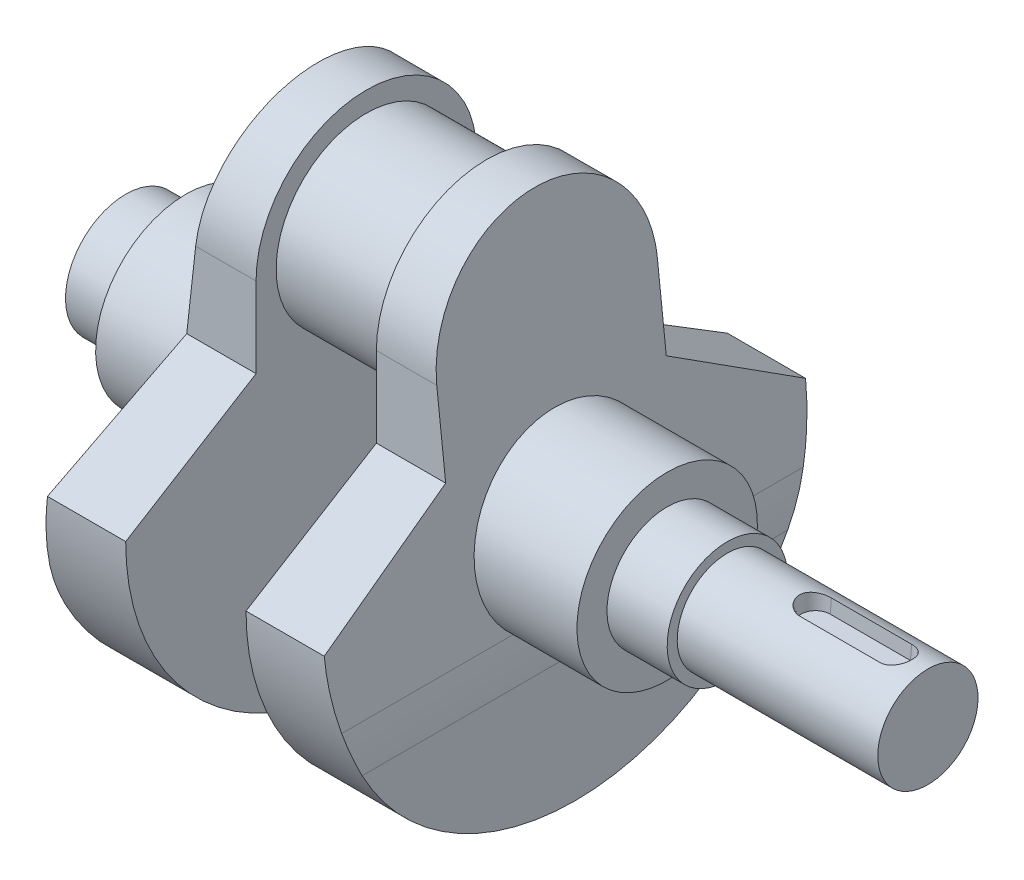
SolidWorks part; units mm, degrees
ref_plane "Front Plane" through (0, 0, 0) normal (0, 0, 1) x (1, 0, 0)
ref_plane "Top Plane" through (0, 0, 0) normal (0, 1, 0) x (1, 0, 0)
ref_plane "Right Plane" through (0, 0, 0) normal (1, 0, 0) x (0, 0, -1)
sketch "Sketch1" plane through (0, 0, 0) normal (1, 0, 0) x (0, 0, -1)
  circle A0 centre (0, 0) radius 22.5
  dimension "D1" = 45
extrude "Boss-Extrude1" add sketch "Sketch1" along normal blind 15
sketch "Sketch2" plane through (15, 0, 0) normal (1, 0, 0) x (0, 0, -1)
  line L0 (-27.5, 0) -> (-27.5, -20)
  line L1 (-27.5, -20) -> (-60, -40)
  line L2 (0, 0) -> (0, -100) construction
  line L3 (27.5, -20) -> (60, -40)
  line L4 (27.5, 0) -> (27.5, -20)
  arc A0 (27.5, 0) -> (-27.5, 0) centre (0, 0) ccw
  arc A1 (-60, -40) -> (60, -40) centre (0, -40) ccw
  dimension "D1" = 120
  dimension "D3" = 55
  dimension "D2" = 40
  dimension "D4" = 20
extrude "Boss-Extrude2" add sketch "Sketch2" along normal blind 22 contours L1 A1 L3 L4 A0 L0
sketch "Sketch3" plane through (0, 0, 0) normal (0, 0, 1) x (1, 0, 0)
  line L0 (27, 27.5) -> (37, 27.5)
  line L1 (37, 27.5) -> (15, 27.5) construction
  line L2 (37, 27.5) -> (37, -62.5)
  line L3 (37, -100) -> (37, -40) construction
  line L4 (37, -62.5) -> (27, 27.5)
  dimension "D1" = 10
  dimension "D2" = 90
extrude "Cut-Extrude1" cut sketch "Sketch3" against normal through all both and the other way through all
fillet "Fillet1" radius 100 1 edges at (37, -62.5, 0)
sketch "Sketch4" plane through (0, 0, 0) normal (0, 0, 1) x (1, 0, 0)
  line L0 (37, -100) -> (37, 0) construction
  line L1 (37, 0) -> (0, 0) construction
  line L2 (25.7901, -17.5) -> (60, -17.5)
  line L3 (60, -17.5) -> (60, -25)
  line L4 (60, -25) -> (75, -25)
  line L5 (75, -25) -> (75, -27.5)
  line L6 (75, -27.5) -> (125, -27.5)
  line L7 (125, -27.5) -> (125, -40)
  line L8 (125, -40) -> (25.7901, -40)
  line L9 (25.7901, -40) -> (25.7901, -17.5)
  line L10 (34.5, -40) -> (-8.8823, -40) construction
  line L11 (36.3884, -56.9954) -> (34.5, -40) construction
  dimension "D1" = 40
  dimension "D2" = 45
  dimension "D3" = 30
  dimension "D4" = 25
  dimension "D5" = 50
  dimension "D6" = 15
  dimension "D7" = 60
revolve "Revolve1" add sketch "Sketch4" angle 360 about L8
sketch "Sketch5" plane through (0, 0, 0) normal (0, 1, 0) x (1, 0, 0)
  line L0 (125, 0) -> (100.4985, 0) construction
  line L1 (125, -12.5) -> (125, 12.5) construction
  line L2 (100.4985, 0) -> (75, 0) construction
  line L3 (75, -15) -> (75, 15) construction
  line L4 (97, 0) -> (117, 0) construction
  line L5 (97, 4) -> (117, 4)
  line L6 (97, -4) -> (117, -4)
  arc A0 (97, 4) -> (97, -4) centre (97, 0) ccw
  arc A1 (117, -4) -> (117, 4) centre (117, 0) ccw
  point P10 (107, 0)
  point P15 (0, 0)
  point P16 (0, 0)
  dimension "D2" = 4
  dimension "D1" = 20
  dimension "D3" = 8
extrude "Cut-Extrude2" cut sketch "Sketch5" against normal blind 4 draft 5 from offset 27.5 offset against normal yes
mirror "Mirror1" about plane through (0, 0, 0) normal (1, 0, 0) of bodies 105
sketch "Sketch6" plane through (0, 0, 0) normal (0, 0, 1) x (1, 0, 0)
  line L0 (-75, -67.6357) -> (-75, -7.5583)
extrude "Cut-Extrude3" cut sketch "Sketch6" against normal through all both and the other way through all
